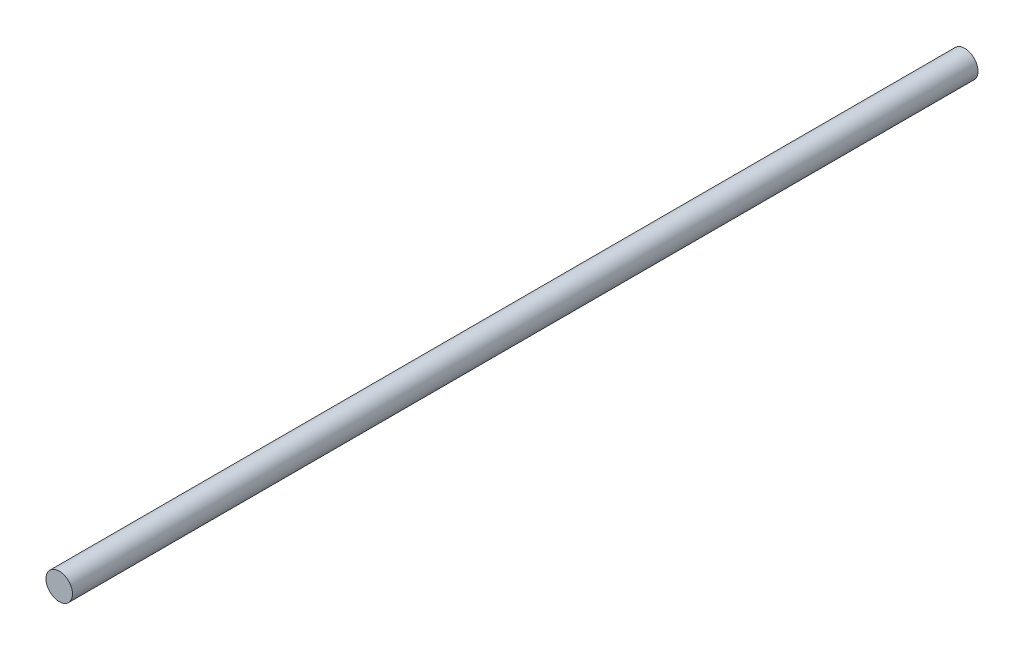
SolidWorks part; units mm, degrees
ref_plane "Front Plane" through (0, 0, 0) normal (0, 0, 1) x (1, 0, 0)
ref_plane "Top Plane" through (0, 0, 0) normal (0, 1, 0) x (1, 0, 0)
ref_plane "Right Plane" through (0, 0, 0) normal (1, 0, 0) x (0, 0, -1)
sketch "Sketch1" plane through (0, 0, 0) normal (0, 0, 1) x (1, 0, 0)
  circle A0 centre (0, 0) radius 3
  dimension "D1" = 6
extrude "Boss-Extrude1" add sketch "Sketch1" along normal blind 205
